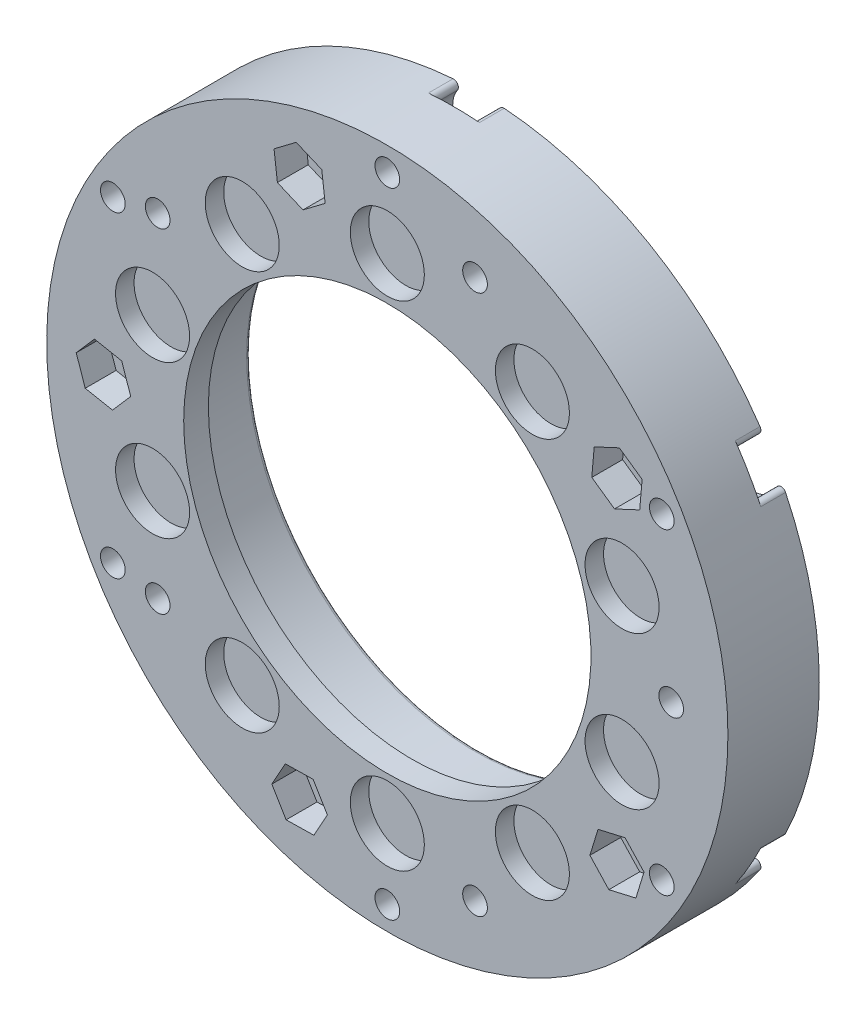
SolidWorks part; units mm, degrees
ref_plane "前视基准面" through (0, 0, 0) normal (0, 0, 1) x (1, 0, 0)
ref_plane "上视基准面" through (0, 0, 0) normal (0, 1, 0) x (1, 0, 0)
ref_plane "右视基准面" through (0, 0, 0) normal (1, 0, 0) x (0, 0, -1)
sketch "草图1" plane through (0, 0, 0) normal (0, 0, 1) x (1, 0, 0)
  circle A0 centre (0, 0) radius 27.6
  dimension "D1" = 55.2
extrude "凸台-拉伸1" add sketch "草图1" along normal blind 5.5
sketch "草图2" plane through (0, 0, 5.5) normal (0, 0, 1) x (1, 0, 0)
  circle A0 centre (0, 0) radius 20 construction
  circle A1 centre (0, 20) radius 3
  circle A2 centre (11.7557, 16.1803) radius 3
  circle A3 centre (19.0211, 6.1803) radius 3
  circle A4 centre (19.0211, -6.1803) radius 3
  circle A5 centre (11.7557, -16.1803) radius 3
  circle A6 centre (0, -20) radius 3
  circle A7 centre (-11.7557, -16.1803) radius 3
  circle A8 centre (-19.0211, -6.1803) radius 3
  circle A9 centre (-19.0211, 6.1803) radius 3
  circle A10 centre (-11.7557, 16.1803) radius 3
  point P25 (0, 0)
  dimension "D1" = 40
  dimension "D2" = 6
  dimension "D3" = 10
extrude "切除-拉伸1" cut sketch "草图2" against normal blind 1.5
sketch "草图5" plane through (0, 0, 0) normal (0, 0, -1) x (-1, 0, 0)
  circle A0 centre (0, 0) radius 18.5
  dimension "D1" = 37
extrude "切除-拉伸3" cut sketch "草图5" against normal blind 3.5
sketch "草图7" plane through (0, 0, 3.5) normal (0, 0, -1) x (-1, 0, 0)
  circle A0 centre (0, 0) radius 16.5
  dimension "D1" = 33
extrude "切除-拉伸8" cut sketch "草图7" against normal through all both and the other way through all
sketch "草图8" plane through (0, 0, 0) normal (0, 0, -1) x (-1, 0, 0)
  circle A0 centre (0, 0) radius 18.5
  circle A1 centre (0, 0) radius 27.6
extrude "凸台-拉伸3" add sketch "草图8" along normal blind 0.5
sketch "草图9" plane through (0, 0, 5.5) normal (0, 0, 1) x (1, 0, 0)
  line L0 (0, 0) -> (8.5468, 24.216) construction
  circle A0 centre (8.5468, 24.216) radius 1
  circle A1 centre (25.2451, 4.7062) radius 1
  circle A2 centre (16.6983, -19.5098) radius 1
  circle A3 centre (-8.5468, -24.216) radius 1
  circle A4 centre (-25.2451, -4.7062) radius 1
  circle A5 centre (-16.6983, 19.5098) radius 1
  point P17 (0, 0)
  dimension "D2" = 2
  dimension "D1" = 25.68
  dimension "D3" = 6
extrude "切除-拉伸9" cut sketch "草图9" against normal through all both and the other way through all
sketch "草图10" plane through (0, 0, -0.5) normal (0, 0, -1) x (-1, 0, 0)
  circle A0 centre (0, 0) radius 18.5
  circle A1 centre (0, 0) radius 27.6
  circle A2 centre (-8.5468, 24.216) radius 1
  circle A3 centre (16.6983, 19.5098) radius 1
  circle A4 centre (25.2451, -4.7062) radius 1
  circle A5 centre (8.5468, -24.216) radius 1
  circle A6 centre (-16.6983, -19.5098) radius 1
  circle A7 centre (-25.2451, 4.7062) radius 1
  point P19 (0, 0)
  dimension "D1" = 6
extrude "凸台-拉伸4" add sketch "草图10" along normal blind 1.4
sketch "草图11" plane through (0, 0, 5.5) normal (0, 0, 1) x (1, 0, 0)
  circle A0 centre (8.5468, 24.216) radius 1
  circle A1 centre (25.2451, 4.7062) radius 1
  circle A2 centre (16.6983, -19.5098) radius 1
  circle A3 centre (-8.5468, -24.216) radius 1
  circle A4 centre (-25.2451, -4.7062) radius 1
  circle A5 centre (-16.6983, 19.5098) radius 1
  point P15 (0, 0)
  dimension "D1" = 6
extrude "凸台-拉伸5" add sketch "草图11" against normal up to surface (7.4 mm away) up to face at (15.6983, -19.5098, -1.9)
sketch "草图12" plane through (0, 0, 5.5) normal (0, 0, 1) x (1, 0, 0)
  line L0 (0, 0) -> (0, 25.68) construction
  circle A0 centre (0, 25.68) radius 1
  circle A1 centre (22.2395, 12.84) radius 1
  circle A2 centre (22.2395, -12.84) radius 1
  circle A3 centre (0, -25.68) radius 1
  circle A4 centre (-22.2395, -12.84) radius 1
  circle A5 centre (-22.2395, 12.84) radius 1
  point P16 (0, 0)
  dimension "D2" = 2
  dimension "D1" = 25.68
  dimension "D3" = 6
extrude "切除-拉伸10" cut sketch "草图12" against normal through all
sketch "草图13" plane through (0, 0, 5.5) normal (0, 0, 1) x (1, 0, 0)
  line L0 (0, 0) -> (0, 20) construction
  line L1 (0, 0) -> (11.7557, 16.1803) construction
  line L2 (0, 20) -> (11.7557, 16.1803) construction
  line L3 (0, 0) -> (7.1074, 21.8743) construction
  line L4 (7.1074, 24.1243) -> (9.0559, 22.9993)
  line L5 (9.0559, 22.9993) -> (9.0559, 20.7493)
  line L6 (9.0559, 20.7493) -> (7.1074, 19.6243)
  line L7 (7.1074, 19.6243) -> (5.1588, 20.7493)
  line L8 (5.1588, 20.7493) -> (5.1588, 22.9993)
  line L9 (5.1588, 22.9993) -> (7.1074, 24.1243)
  line L10 (23.4678, 2.2008) -> (25.1399, 0.6953)
  line L11 (25.1399, 0.6953) -> (24.6721, -1.5055)
  line L12 (24.6721, -1.5055) -> (22.5322, -2.2008)
  line L13 (22.5322, -2.2008) -> (20.8601, -0.6953)
  line L14 (20.8601, -0.6953) -> (21.3279, 1.5055)
  line L15 (21.3279, 1.5055) -> (23.4678, 2.2008)
  line L16 (9.3451, -21.6391) -> (8.4299, -23.6946)
  line L17 (8.4299, -23.6946) -> (6.1922, -23.9298)
  line L18 (6.1922, -23.9298) -> (4.8697, -22.1095)
  line L19 (4.8697, -22.1095) -> (5.7849, -20.054)
  line L20 (5.7849, -20.054) -> (8.0225, -19.8188)
  line L21 (8.0225, -19.8188) -> (9.3451, -21.6391)
  line L22 (-17.6922, -15.5745) -> (-19.9299, -15.3393)
  line L23 (-19.9299, -15.3393) -> (-20.8451, -13.2839)
  line L24 (-20.8451, -13.2839) -> (-19.5225, -11.4636)
  line L25 (-19.5225, -11.4636) -> (-17.2849, -11.6988)
  line L26 (-17.2849, -11.6988) -> (-16.3697, -13.7542)
  line L27 (-16.3697, -13.7542) -> (-17.6922, -15.5745)
  line L28 (-20.2795, 12.0135) -> (-20.7473, 14.2143)
  line L29 (-20.7473, 14.2143) -> (-19.0752, 15.7199)
  line L30 (-19.0752, 15.7199) -> (-16.9353, 15.0246)
  line L31 (-16.9353, 15.0246) -> (-16.4675, 12.8238)
  line L32 (-16.4675, 12.8238) -> (-18.1396, 11.3182)
  line L33 (-18.1396, 11.3182) -> (-20.2795, 12.0135)
  circle A0 centre (7.1074, 21.8743) radius 2.25 construction
  point P8 (7.1074, 24.1243)
  point P11 (9.0559, 22.9993)
  point P12 (9.0559, 20.7493)
  point P13 (7.1074, 19.6243)
  point P14 (5.1588, 20.7493)
  point P15 (5.1588, 22.9993)
  point P16 (7.1074, 21.8743)
  point P48 (0, 0)
  dimension "D2" = 4.5
  dimension "D1" = 23
  dimension "D3" = 6
  dimension "D4" = 5
extrude "切除-拉伸11" cut sketch "草图13" against normal blind 2
sketch "草图15" plane through (0, 0, 3.5) normal (0, 0, 1) x (1, 0, 0)
  line L0 (-20.2795, 12.0135) -> (-16.9353, 15.0246) construction
  circle A0 centre (-18.6074, 13.5191) radius 1
  circle A1 centre (7.1074, 21.8743) radius 1
  circle A2 centre (23, 0) radius 1
  circle A3 centre (7.1074, -21.8743) radius 1
  circle A4 centre (-18.6074, -13.5191) radius 1
  point P16 (0, 0)
  dimension "D1" = 2
  dimension "D2" = 5
extrude "切除-拉伸12" cut sketch "草图15" against normal through all both and the other way through all
sketch "草图16" plane through (0, 0, 5.5) normal (0, 0, 1) x (1, 0, 0)
  line L0 (-11.7557, 16.1803) -> (0, 20) construction
  line L1 (0, 0) -> (-7.1074, 21.8743) construction
  circle A0 centre (-7.1074, 21.8743) radius 1
  circle A1 centre (18.6074, 13.5191) radius 1
  circle A2 centre (18.6074, -13.5191) radius 1
  circle A3 centre (-7.1074, -21.8743) radius 1
  circle A4 centre (-23, 0) radius 1
  point P18 (0, 0)
  dimension "D2" = 2
  dimension "D1" = 23
  dimension "D3" = 5
extrude "切除-拉伸13" cut sketch "草图16" against normal through all both and the other way through all
sketch "草图18" plane through (0, 0, 5.5) normal (0, 0, 1) x (1, 0, 0)
  line L0 (7.1074, 24.1243) -> (9.0559, 22.9993)
  line L1 (9.0559, 22.9993) -> (9.0559, 20.7493)
  line L2 (9.0559, 20.7493) -> (7.1074, 19.6243)
  line L3 (7.1074, 19.6243) -> (5.1588, 20.7493)
  line L4 (5.1588, 20.7493) -> (5.1588, 22.9993)
  line L5 (5.1588, 22.9993) -> (7.1074, 24.1243)
  line L6 (23.4678, 2.2008) -> (25.1399, 0.6953)
  line L7 (25.1399, 0.6953) -> (24.6721, -1.5055)
  line L8 (24.6721, -1.5055) -> (22.5322, -2.2008)
  line L9 (22.5322, -2.2008) -> (20.8601, -0.6953)
  line L10 (20.8601, -0.6953) -> (21.3279, 1.5055)
  line L11 (21.3279, 1.5055) -> (23.4678, 2.2008)
  line L12 (9.3451, -21.6391) -> (8.4299, -23.6946)
  line L13 (8.4299, -23.6946) -> (6.1922, -23.9298)
  line L14 (6.1922, -23.9298) -> (4.8697, -22.1095)
  line L15 (4.8697, -22.1095) -> (5.7849, -20.054)
  line L16 (5.7849, -20.054) -> (8.0225, -19.8188)
  line L17 (8.0225, -19.8188) -> (9.3451, -21.6391)
  line L18 (-17.6922, -15.5745) -> (-19.9299, -15.3393)
  line L19 (-19.9299, -15.3393) -> (-20.8451, -13.2839)
  line L20 (-20.8451, -13.2839) -> (-19.5225, -11.4636)
  line L21 (-19.5225, -11.4636) -> (-17.2849, -11.6988)
  line L22 (-17.2849, -11.6988) -> (-16.3697, -13.7542)
  line L23 (-16.3697, -13.7542) -> (-17.6922, -15.5745)
  line L24 (-20.2795, 12.0135) -> (-20.7473, 14.2143)
  line L25 (-20.7473, 14.2143) -> (-19.0752, 15.7199)
  line L26 (-19.0752, 15.7199) -> (-16.9353, 15.0246)
  line L27 (-16.9353, 15.0246) -> (-16.4675, 12.8238)
  line L28 (-16.4675, 12.8238) -> (-18.1396, 11.3182)
  line L29 (-18.1396, 11.3182) -> (-20.2795, 12.0135)
  circle A0 centre (7.1074, 21.8743) radius 1
  circle A1 centre (23, 0) radius 1
  circle A2 centre (7.1074, -21.8743) radius 1
  circle A3 centre (-18.6074, -13.5191) radius 1
  circle A4 centre (-18.6074, 13.5191) radius 1
  point P49 (0, 0)
  dimension "D1" = 5
extrude "凸台-拉伸6" add sketch "草图18" against normal up to surface (2 mm away) up to face at (6.1074, 21.8743, 3.5)
sketch "草图19" plane through (0, 0, 5.5) normal (0, 0, 1) x (1, 0, 0)
  line L0 (-8.9043, 20.5202) -> (-9.1785, 22.7534)
  line L1 (-9.1785, 22.7534) -> (-7.3817, 24.1075)
  line L2 (-7.3817, 24.1075) -> (-5.3105, 23.2284)
  line L3 (-5.3105, 23.2284) -> (-5.0362, 20.9952)
  line L4 (-5.0362, 20.9952) -> (-6.8331, 19.6411)
  line L5 (-6.8331, 19.6411) -> (-8.9043, 20.5202)
  line L6 (16.5682, 12.5681) -> (16.7643, 14.8096)
  line L7 (16.7643, 14.8096) -> (18.8034, 15.7605)
  line L8 (18.8034, 15.7605) -> (20.6466, 14.47)
  line L9 (20.6466, 14.47) -> (20.4505, 12.2286)
  line L10 (20.4505, 12.2286) -> (18.4113, 11.2776)
  line L11 (18.4113, 11.2776) -> (16.5682, 12.5681)
  line L12 (17.0729, -11.8736) -> (19.2652, -11.3674)
  line L13 (19.2652, -11.3674) -> (20.7997, -13.0129)
  line L14 (20.7997, -13.0129) -> (20.1419, -15.1646)
  line L15 (20.1419, -15.1646) -> (17.9496, -15.6708)
  line L16 (17.9496, -15.6708) -> (16.4151, -14.0253)
  line L17 (16.4151, -14.0253) -> (17.0729, -11.8736)
  line L18 (-6.0166, -19.9064) -> (-4.8577, -21.835)
  line L19 (-4.8577, -21.835) -> (-5.9485, -23.8029)
  line L20 (-5.9485, -23.8029) -> (-8.1982, -23.8422)
  line L21 (-8.1982, -23.8422) -> (-9.357, -21.9136)
  line L22 (-9.357, -21.9136) -> (-8.2663, -19.9457)
  line L23 (-8.2663, -19.9457) -> (-6.0166, -19.9064)
  line L24 (-20.7913, -0.4293) -> (-22.2674, -2.1274)
  line L25 (-22.2674, -2.1274) -> (-24.4761, -1.6981)
  line L26 (-24.4761, -1.6981) -> (-25.2087, 0.4293)
  line L27 (-25.2087, 0.4293) -> (-23.7326, 2.1274)
  line L28 (-23.7326, 2.1274) -> (-21.5239, 1.6981)
  line L29 (-21.5239, 1.6981) -> (-20.7913, -0.4293)
  circle A0 centre (-7.1074, 21.8743) radius 2.25 construction
  point P3 (-8.9043, 20.5202)
  point P6 (-9.1785, 22.7534)
  point P7 (-7.3817, 24.1075)
  point P8 (-5.3105, 23.2284)
  point P9 (-5.0362, 20.9952)
  point P10 (-6.8331, 19.6411)
  point P11 (-7.1074, 21.8743)
  point P42 (0, 0)
  dimension "D1" = 4.5
  dimension "D2" = 6
  dimension "D3" = 5
extrude "切除-拉伸15" cut sketch "草图19" against normal blind 2.5
sketch "草图20" plane through (0, 0, -1.9) normal (0, 0, -1) x (-1, 0, 0)
  circle A0 centre (0, 25.68) radius 2.1
  circle A1 centre (22.2395, 12.84) radius 2.1
  circle A2 centre (22.2395, -12.84) radius 2.1
  circle A3 centre (0, -25.68) radius 2.1
  circle A4 centre (-22.2395, -12.84) radius 2.1
  circle A5 centre (-22.2395, 12.84) radius 2.1
  point P15 (0, 0)
  dimension "D1" = 4.2
  dimension "D2" = 6
extrude "切除-拉伸16" cut sketch "草图20" against normal blind 2
fillet "圆角2" radius 0.4 12 edges at (23.4492, -14.5566, -0.9) (24.331, -13.0293, -0.9) (-0.8818, -27.5859, -0.9) (0.8818, -27.5859, -0.9) (-24.331, -13.0293, -0.9) (-23.4492, -14.5566, -0.9) (-23.4492, 14.5566, -0.9) (-24.331, 13.0293, -0.9) (0.8818, 27.5859, -0.9) (-0.8818, 27.5859, -0.9) (24.331, 13.0293, -0.9) (23.4492, 14.5566, -0.9)
sketch "草图21" plane through (0, 0, -1.9) normal (0, 0, -1) x (-1, 0, 0)
  circle A0 centre (18.6074, 13.5191) radius 1.9
  circle A1 centre (18.6074, -13.5191) radius 1.9
  circle A2 centre (-7.1074, -21.8743) radius 1.9
  circle A3 centre (-23, 0) radius 1.9
  circle A4 centre (-7.1074, 21.8743) radius 1.9
  point P13 (0, 0)
  dimension "D1" = 3.8
  dimension "D2" = 5
extrude "切除-拉伸17" cut sketch "草图21" against normal blind 2
fillet "圆角3" radius 0.3 4 edges at (-20.4576, 13.9512, -0.9) (-20.1765, 12.4477, -0.9) (-20.1765, -12.4477, -0.9) (-20.4576, -13.9512, -0.9)
fillet "圆角4" radius 0.3 1 edges at (-18.5, 0, -1.9)
